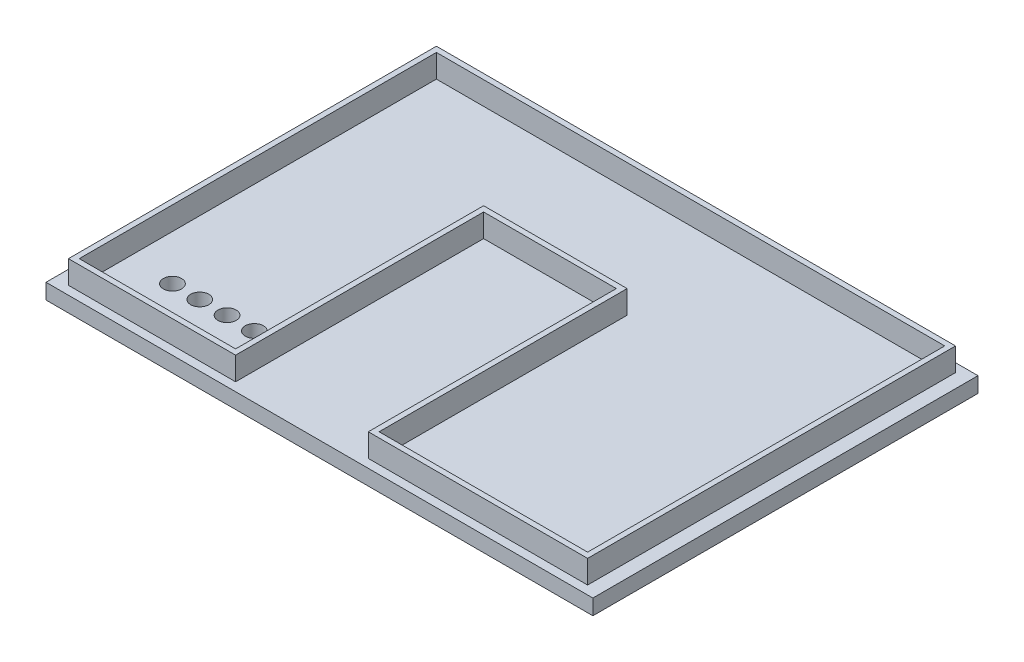
SolidWorks part; units mm, degrees
ref_plane "Front" through (0, 0, 0) normal (0, 0, 1) x (1, 0, 0)
ref_plane "Top" through (0, 0, 0) normal (0, 1, 0) x (1, 0, 0)
ref_plane "Right" through (0, 0, 0) normal (1, 0, 0) x (0, 0, -1)
sketch "Sketch1" plane through (0, 0, 0) normal (0, 1, 0) x (1, 0, 0)
  line L1 (0, 0) -> (180.34, 0)
  line L2 (0, 0) -> (0, 127)
  line L3 (0, 127) -> (180.34, 127)
  line L4 (180.34, 0) -> (180.34, 127)
  dimension "D1" = 180.34
  dimension "D2" = 127
extrude "Boss-Extrude1" add sketch "Sketch1" along normal blind 5.08 contours L2 L3 L4 L1
sketch "Sketch2" plane through (0, 5.08, 0) normal (0, 1, 0) x (1, 0, 0)
  line L0 (0, 0) -> (0, 127) construction
  line L1 (4.572, 124.1679) -> (175.768, 124.1679)
  line L2 (4.572, 124.1679) -> (4.572, 2.8321)
  line L3 (59.69, 84.6201) -> (59.69, 2.8321)
  line L4 (175.768, 124.1679) -> (175.768, 2.8321)
  line L5 (0, 127) -> (180.34, 127) construction
  line L7 (59.69, 84.6201) -> (103.4542, 84.6201)
  line L8 (59.69, 2.8321) -> (4.572, 2.8321)
  line L9 (4.572, 2.8321) -> (7.0589, -2.4012)
  line L11 (103.4542, 84.6201) -> (103.4542, 2.8321)
  line L12 (103.4542, 2.8321) -> (175.768, 2.8321)
  line L14 (6.35, 122.3899) -> (6.35, 4.6101)
  line L15 (6.35, 4.6101) -> (57.912, 4.6101)
  line L16 (57.912, 4.6101) -> (57.912, 86.3981)
  line L17 (57.912, 86.3981) -> (105.2322, 86.3981)
  line L18 (105.2322, 86.3981) -> (105.2322, 4.6101)
  line L19 (105.2322, 4.6101) -> (173.99, 4.6101)
  line L20 (173.99, 4.6101) -> (173.99, 122.3899)
  line L21 (173.99, 122.3899) -> (6.35, 122.3899)
  point P4 (4.572, 63.5)
  point P7 (0, 63.5)
  point P8 (90.17, 124.1679)
  point P11 (90.17, 127)
  dimension "D1" = 171.196
  dimension "D2" = 121.3358
  dimension "D3" = 121.3358
  dimension "D4" = 72.3138
  dimension "D5" = 55.118
  dimension "D6" = 81.788
  dimension "D7" = 1.778
  dimension "D8" = 1.778
  dimension "D9" = 1.778
  dimension "D10" = 1.778
  dimension "D11" = 1.778
  dimension "D12" = 1.778
  dimension "D13" = 1.778
  dimension "D14" = 1.778
extrude "Boss-Extrude2" add sketch "Sketch2" along normal blind 7.62 contours L8 L3 L7 L11 L12 L4 L1 L2 | L14 L15 L16 L17 L18 L19 L20 L21
sketch "Sketch3" plane through (0, 0, 0) normal (0, -1, 0) x (1, 0, 0)
  line L0 (0, 0) -> (0, -127) construction
  line L1 (0, 0) -> (180.34, 0) construction
  circle A0 centre (21.26, -20.4409) radius 3
  circle A1 centre (30.26, -20.4409) radius 3
  circle A2 centre (39.26, -20.4409) radius 3
  circle A3 centre (48.26, -20.4409) radius 3
  dimension "D1" = 6
  dimension "D2" = 6
  dimension "D3" = 6
  dimension "D4" = 6
  dimension "D6" = 9
  dimension "D5" = 9
  dimension "D7" = 9
  dimension "D8" = 48.26
  dimension "D9" = 20.4409
extrude "Cut-Extrude1" cut sketch "Sketch3" against normal blind 10.16
